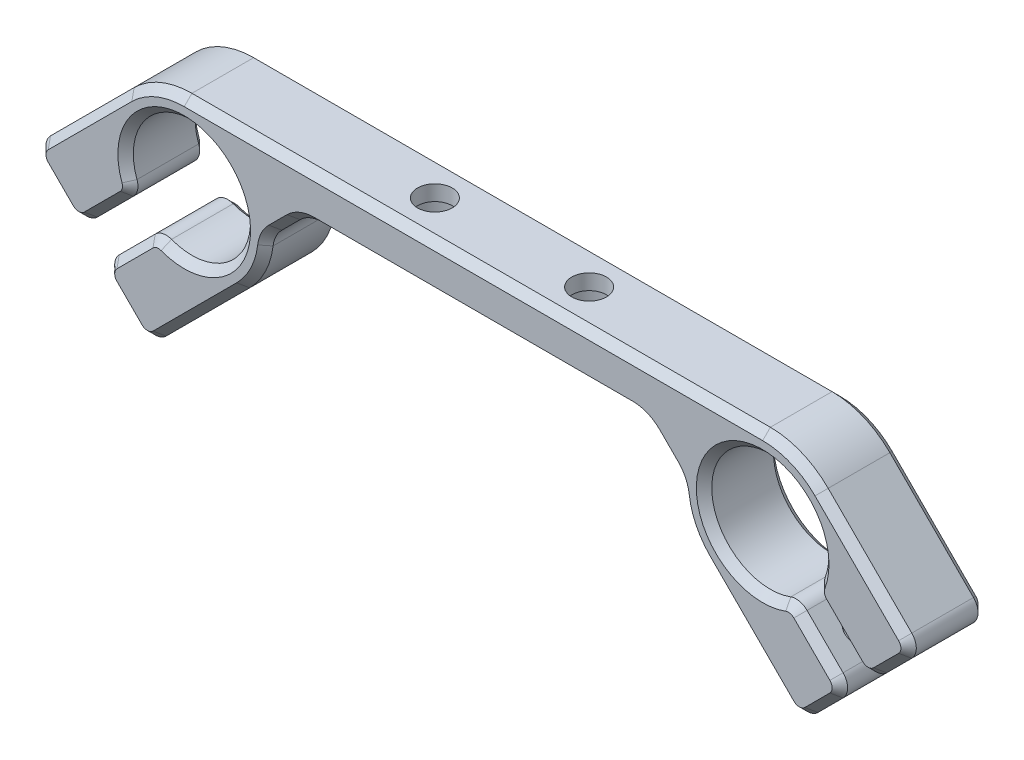
SolidWorks part; units mm, degrees
material "Сплав 2024"
ref_plane "Спереди" through (0, 0, 0) normal (0, 0, 1) x (1, 0, 0)
ref_plane "Сверху" through (0, 0, 0) normal (0, 1, 0) x (1, 0, 0)
ref_plane "Справа" through (0, 0, 0) normal (1, 0, 0) x (0, 0, -1)
sketch "Эскиз1" plane through (0, 0, 0) normal (0, 0, 1) x (1, 0, 0)
  line L0 (-108.1441, 0) -> (120.4788, 0) construction
  line L1 (-20.2307, 17.2693) -> (-60.5817, -23.0817) construction
  line L2 (-44.9953, 7.4953) -> (-57.251, -4.7603)
  line L3 (-57.251, -4.7603) -> (-51.1699, -10.8414)
  line L4 (-51.1699, -10.8414) -> (-44.0988, -3.7704)
  line L5 (-30.0047, -7.4953) -> (-42.2603, -19.751)
  line L6 (-48.3414, -13.6699) -> (-41.2704, -6.5988)
  line L7 (-42.2603, -19.751) -> (-48.3414, -13.6699)
  line L8 (-54.4567, 10.6) -> (67.3125, 10.6) construction
  line L9 (-37.5, 10.6) -> (37.5, 10.6)
  line L10 (0, 19.8914) -> (0, -20.2986) construction
  line L11 (-26.9, 0) -> (-22.3, 4.6)
  line L12 (-52.7336, 4.6) -> (84.69, 4.6) construction
  line L13 (-22.3, 4.6) -> (22.3, 4.6)
  line L14 (26.9, 0) -> (22.3, 4.6)
  line L15 (30.0047, -7.4953) -> (42.2603, -19.751)
  line L16 (42.2603, -19.751) -> (48.3414, -13.6699)
  line L17 (48.3414, -13.6699) -> (41.2704, -6.5988)
  line L18 (51.1699, -10.8414) -> (44.0988, -3.7704)
  line L19 (57.251, -4.7603) -> (51.1699, -10.8414)
  line L20 (44.9953, 7.4953) -> (57.251, -4.7603)
  arc A0 (-41.2704, -6.5988) -> (-44.0988, -3.7704) centre (-37.5, 0) ccw
  arc A1 (-30.0047, -7.4953) -> (-26.9, 0) centre (-37.5, 0) ccw
  arc A2 (-37.5, 10.6) -> (-44.9953, 7.4953) centre (-37.5, 0) ccw
  circle A3 centre (-37.5, 0) radius 10.6 construction
  circle A4 centre (-37.5, 0) radius 7.6 construction
  arc A5 (30.0047, -7.4953) -> (26.9, 0) centre (37.5, 0) cw
  arc A6 (41.2704, -6.5988) -> (44.0988, -3.7704) centre (37.5, 0) cw
  arc A7 (37.5, 10.6) -> (44.9953, 7.4953) centre (37.5, 0) cw
  point P11 (-44.0988, -3.7704)
  point P18 (-26.9, 0)
  point P20 (-30.2321, 2.222)
  point P32 (0, 4.6)
  point P43 (0, 10.6)
  dimension "D1" = 15.2
  dimension "D2" = 37.5
  dimension "D3" = 3
  dimension "D4" = 45
  dimension "D5" = 2
  dimension "D6" = 10
  dimension "D7" = 6
extrude "Бобышка-Вытянуть1" add sketch "Эскиз1" along normal blind 10
sketch "Эскиз2" plane through (-11.2547, 11.2547, 0) normal (0.7071, -0.7071, 0) x (0, 0, -1)
  line L0 (-5, -43.8486) -> (-5, -26.5165) construction
  line L1 (-10, -43.8486) -> (0, -43.8486) construction
  line L2 (-10, -26.5165) -> (0, -26.5165) construction
  line L3 (-10, -38.8486) -> (0, -38.8486) construction
  line L4 (-10, -43.8486) -> (-10, -26.5165) construction
  line L5 (0, -43.8486) -> (0, -26.5165) construction
  dimension "D1" = 5
sketch "Эскиз3" plane through (11.2547, 11.2547, 0) normal (-0.7071, -0.7071, 0) x (0, 0, 1)
  line L0 (5, -43.8486) -> (5, -26.5165) construction
  line L1 (10, -43.8486) -> (0, -43.8486) construction
  line L2 (10, -26.5165) -> (0, -26.5165) construction
  line L3 (10, -38.8486) -> (0, -38.8486) construction
  line L4 (10, -26.5165) -> (10, -43.8486) construction
  line L5 (0, -26.5165) -> (0, -43.8486) construction
  dimension "D1" = 5
hole_wizard "Отверстие обработанное метчиком M4x0.71" positions "Эскиз5" profile "Эскиз4" tap size "M4x0.7" standard "Ansi Metric"
sketch "Эскиз5" plane through (11.2547, 11.2547, 0) normal (-0.7071, -0.7071, 0) x (0, 0, 1)
  line L0 (5, -43.8486) -> (5, -26.5165) construction
  line L1 (10, -38.8486) -> (0, -38.8486) construction
  point P0 (5, -38.8486)
sketch "Эскиз4" plane through (38.7248, -16.2155, 5) normal (0, 0, 1) x (0.7071, -0.7071, 0)
  line L0 (0, 0) -> (0, 19.9914)
  line L1 (0, 19.9914) -> (1.65, 19)
  line L2 (1.65, 19) -> (1.65, 0)
  line L5 (1.65, 0) -> (0, 0)
  line L10 (0, 19.9914) -> (-1.65, 19) construction
  line L11 (0, -6.35) -> (0, 107.95) construction
  dimension "Диаметр сверла" = 3.3
  dimension "Глубина сверла" = 19
  dimension "Угол заточки сверла" = 118
cosmetic thread "Отверстие резьбы1" parameters "D1"=19, "D2"=4
hole_wizard "Отверстие обработанное метчиком M4x0.72" positions "Эскиз7" profile "Эскиз6" tap size "M4x0.7" standard "Ansi Metric"
sketch "Эскиз7" plane through (-11.2547, 11.2547, 0) normal (0.7071, -0.7071, 0) x (0, 0, -1)
  line L0 (-5, -43.8486) -> (-5, -26.5165) construction
  line L1 (-10, -38.8486) -> (0, -38.8486) construction
  point P0 (-5, -38.8486)
sketch "Эскиз6" plane through (-38.7248, -16.2155, 5) normal (0, 0, 1) x (0.7071, 0.7071, 0)
  line L0 (0, 0) -> (0, 19.9914)
  line L1 (0, 19.9914) -> (1.65, 19)
  line L2 (1.65, 19) -> (1.65, 0)
  line L5 (1.65, 0) -> (0, 0)
  line L10 (0, 19.9914) -> (-1.65, 19) construction
  line L11 (0, -6.35) -> (0, 107.95) construction
  dimension "Диаметр сверла" = 3.3
  dimension "Глубина сверла" = 19
  dimension "Угол заточки сверла" = 118
cosmetic thread "Отверстие резьбы2" parameters "D1"=19, "D2"=4
fillet "Скругление1" radius 2 12 edges at (57.251, -4.7603, 5) (51.1699, -10.8414, 5) (42.2603, -19.751, 5) (48.3414, -13.6699, 5) (44.0988, -3.7704, 5) (41.2704, -6.5988, 5) (-44.0988, -3.7704, 5) (-41.2704, -6.5988, 5) (-57.251, -4.7603, 5) (-51.1699, -10.8414, 5) (-48.3414, -13.6699, 5) (-42.2603, -19.751, 5)
fillet "Скругление2" radius 4 4 edges at (-26.9, 0, 5) (-22.3, 4.6, 5) (26.9, 0, 5) (22.3, 4.6, 5)
chamfer "Фаска1" distance 1 angle 45 76 edges at (41.5564, 9.7931, 0) (0, 10.6, 0) (-41.5564, 9.7931, 0) (-50.4161, 2.0746, 0) (-56.4226, -4.7603, 0) (-54.2104, -7.8009, 0) (-51.1699, -10.013, 0) (-47.4204, -7.092, 0) (-44.5453, -3.7689, 0) (-32.126, 5.374, 0) (-41.2689, -7.0453, 0) (-44.592, -9.9204, 0) (-47.513, -13.6699, 0) (-45.3009, -16.7104, 0) (-42.2603, -18.9226, 0) (-35.4254, -12.9161, 0) (-27.9703, -4.6416, 0) (-26.603, -0.0122, 0) (-24.6535, 2.2465, 0) (-22.1739, 4.2955, 0) (0, 4.6, 0) (22.1739, 4.2955, 0) (24.6535, 2.2465, 0) (26.603, -0.0122, 0) (27.9703, -4.6416, 0) (35.4254, -12.9161, 0) (42.2603, -18.9226, 0) (45.3009, -16.7104, 0) (47.513, -13.6699, 0) (44.592, -9.9204, 0) (41.2689, -7.0453, 0) (32.126, 5.374, 0) (44.5453, -3.7689, 0) (47.4204, -7.092, 0) (51.1699, -10.013, 0) (54.2104, -7.8009, 0) (56.4226, -4.7603, 0) (50.4161, 2.0746, 0) (51.1699, -10.013, 10) (47.4204, -7.092, 10) (44.5453, -3.7689, 10) (32.126, 5.374, 10) (41.2689, -7.0453, 10) (44.592, -9.9204, 10) (47.513, -13.6699, 10) (45.3009, -16.7104, 10) (42.2603, -18.9226, 10) (35.4254, -12.9161, 10) (27.9703, -4.6416, 10) (26.603, -0.0122, 10) (24.6535, 2.2465, 10) (22.1739, 4.2955, 10) (0, 4.6, 10) (-22.1739, 4.2955, 10) (-24.6535, 2.2465, 10) (-26.603, -0.0122, 10) (-27.9703, -4.6416, 10) (-35.4254, -12.9161, 10) (-42.2603, -18.9226, 10) (-45.3009, -16.7104, 10) (-47.513, -13.6699, 10) (-44.592, -9.9204, 10) (-41.2689, -7.0453, 10) (-32.126, 5.374, 10) (-44.5453, -3.7689, 10) (-47.4204, -7.092, 10) (-51.1699, -10.013, 10) (-54.2104, -7.8009, 10) (-56.4226, -4.7603, 10) (-50.4161, 2.0746, 10) (-41.5564, 9.7931, 10) (0, 10.6, 10) (41.5564, 9.7931, 10) (50.4161, 2.0746, 10) (56.4226, -4.7603, 10) (54.2104, -7.8009, 10)
sketch "Эскиз8" plane through (0, 4.6, 0) normal (0, -1, 0) x (1, 0, 0)
  line L0 (-22.3, 5) -> (22.3, 5) construction
  line L1 (-22.3, 10) -> (-22.3, 0) construction
  line L2 (22.3, 10) -> (22.3, 0) construction
  line L3 (-10, 10) -> (-10, 0) construction
  line L4 (-22.3, 10) -> (22.3, 10) construction
  line L5 (-22.3, 0) -> (22.3, 0) construction
  line L6 (10, 10) -> (10, 0) construction
  dimension "D1" = 20
  dimension "D2" = 10
hole_wizard "Цековка для винта с внутренним шестигранником M41" positions "Эскиз10" profile "Эскиз9" counterbore size "M4" standard "Ansi Metric" end condition through all
sketch "Эскиз10" plane through (0, 4.6, 0) normal (0, -1, 0) x (-1, 0, 0)
  line L0 (22.3, -5) -> (-22.3, -5) construction
  line L1 (-10, -10) -> (-10, 0) construction
  line L2 (10, -10) -> (10, 0) construction
  point P0 (10, -5)
  point P2 (-10, -5)
sketch "Эскиз9" plane through (-10, 4.6, 5) normal (1, 0, 0) x (0, 0, -1)
  line L0 (0, 0) -> (0, 6)
  line L1 (0, 6) -> (2.25, 6)
  line L3 (2.25, 6) -> (2.25, 4)
  line L4 (2.25, 4) -> (4, 4)
  line L5 (4, 4) -> (4, 0)
  line L7 (4, 0) -> (0, 0)
  line L11 (0, -6.35) -> (0, 107.95) construction
  dimension "Диаметр сквозного отверстия" = 4.5
  dimension "Глубина сквозного отверстия" = 6
  dimension "Диаметр цековки" = 8
  dimension "Глубина цековки" = 4
